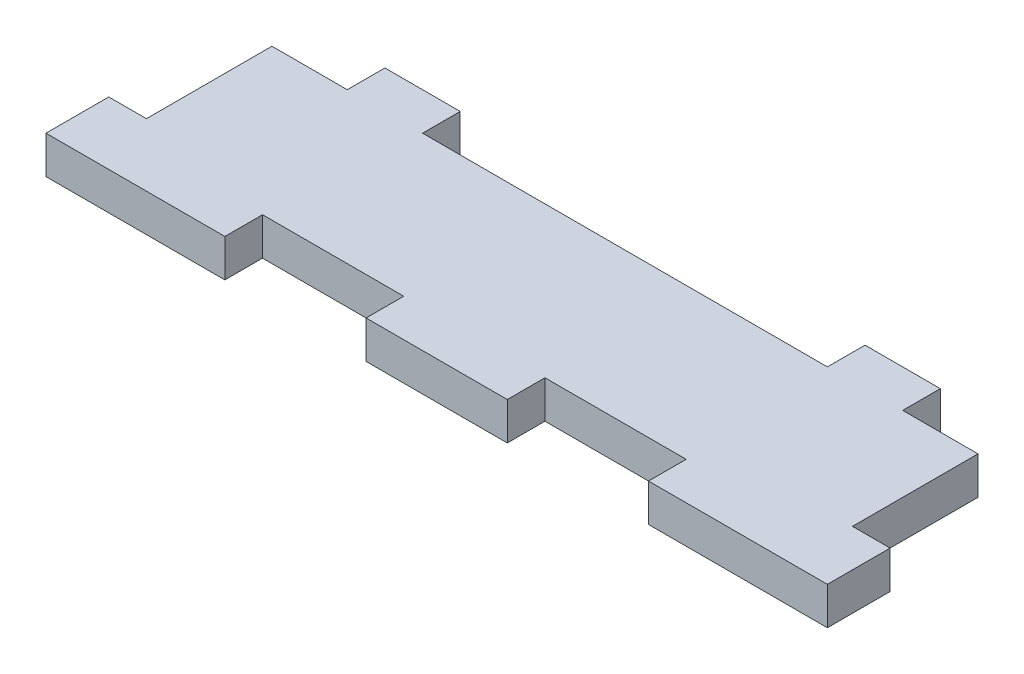
SolidWorks part; units mm, degrees
ref_plane "Front Plane" through (0, 0, 0) normal (0, 0, 1) x (1, 0, 0)
ref_plane "Top Plane" through (0, 0, 0) normal (0, 1, 0) x (1, 0, 0)
ref_plane "Right Plane" through (0, 0, 0) normal (1, 0, 0) x (0, 0, -1)
sketch "Sketch1" plane through (0, 0, 0) normal (0, 1, 0) x (1, 0, 0)
  line L1 (-56.25, -12) -> (56.25, -12)
  line L2 (-56.25, -12) -> (-56.25, 12)
  line L3 (-56.25, 12) -> (56.25, 12)
  line L4 (56.25, -12) -> (56.25, 12)
  line L5 (-56.25, -12) -> (56.25, 12) construction
  line L6 (-56.25, 12) -> (56.25, -12) construction
  point P0 (0, 0)
  dimension "D1" = 112.5
  dimension "D2" = 24
extrude "Boss-Extrude1" add sketch "Sketch1" along normal blind 6
sketch "Sketch2" plane through (0, 0, 12) normal (0, 0, 1) x (1, 0, 0)
  line L0 (-56.25, 6) -> (56.25, 6) construction
  line L1 (-56.25, 0) -> (-33.75, 0)
  line L2 (-56.25, 0) -> (-56.25, 6)
  line L3 (-56.25, 6) -> (-33.75, 6)
  line L4 (-33.75, 0) -> (-33.75, 6)
  line L5 (-56.25, 0) -> (56.25, 0) construction
  line L6 (-33.75, 6) -> (-11.25, 6) construction
  line L7 (-33.75, 6) -> (-33.75, 0) construction
  line L8 (-33.75, 0) -> (-11.25, 0) construction
  line L9 (-11.25, 6) -> (-11.25, 0) construction
  line L11 (-11.25, 0) -> (11.25, 0)
  line L12 (-11.25, 0) -> (-11.25, 6)
  line L13 (-11.25, 6) -> (11.25, 6)
  line L14 (11.25, 0) -> (11.25, 6)
  line L15 (11.25, 6) -> (33.75, 6) construction
  line L16 (11.25, 6) -> (11.25, 0) construction
  line L17 (11.25, 0) -> (33.75, 0) construction
  line L18 (33.75, 6) -> (33.75, 0) construction
  line L19 (33.75, 0) -> (56.25, 0)
  line L20 (33.75, 0) -> (33.75, 6)
  line L21 (33.75, 6) -> (56.25, 6)
  line L22 (56.25, 0) -> (56.25, 6)
extrude "Boss-Extrude2" add sketch "Sketch2" along normal blind 6
sketch "Sketch3" plane through (56.25, 0, 0) normal (1, 0, 0) x (0, 0, -1)
  line L1 (-18, 0) -> (-8, 0)
  line L2 (-18, 0) -> (-18, 6)
  line L3 (-18, 6) -> (-8, 6)
  line L4 (-8, 0) -> (-8, 6)
  line L5 (-18, 6) -> (12, 6) construction
  dimension "D1" = 10
extrude "Boss-Extrude3" add sketch "Sketch3" along normal blind 6
mirror "Mirror1" about plane through (0, 0, 0) normal (1, 0, 0) of "Boss-Extrude3"
sketch "Sketch4" plane through (0, 0, -12) normal (0, 0, -1) x (-1, 0, 0)
  line L0 (-32.25, 0) -> (32.25, 0)
  line L1 (-56.25, 0) -> (56.25, 0) construction
  line L2 (-56.25, 6) -> (56.25, 6) construction
  line L3 (32.25, 0) -> (44.25, 0)
  line L4 (32.25, 0) -> (32.25, 6)
  line L5 (32.25, 6) -> (44.25, 6)
  line L6 (44.25, 0) -> (44.25, 6)
  line L7 (-32.25, 0) -> (-32.25, 6) construction
  line L8 (-32.25, 0) -> (-44.25, 0)
  line L9 (-32.25, 0) -> (-32.25, 6)
  line L10 (-32.25, 6) -> (-44.25, 6)
  line L11 (-44.25, 0) -> (-44.25, 6)
  line L12 (44.25, 6) -> (44.25, 0) construction
  point P5 (0, 0)
  line M9 (-56.25, 0) -> (56.25, 0)
  line M11 (56.25, 6) -> (-56.25, 6)
extrude "Boss-Extrude4" add sketch "Sketch4" along normal blind 6 contours L11 L9 M9 M11 | L6 L4 M9 M11
